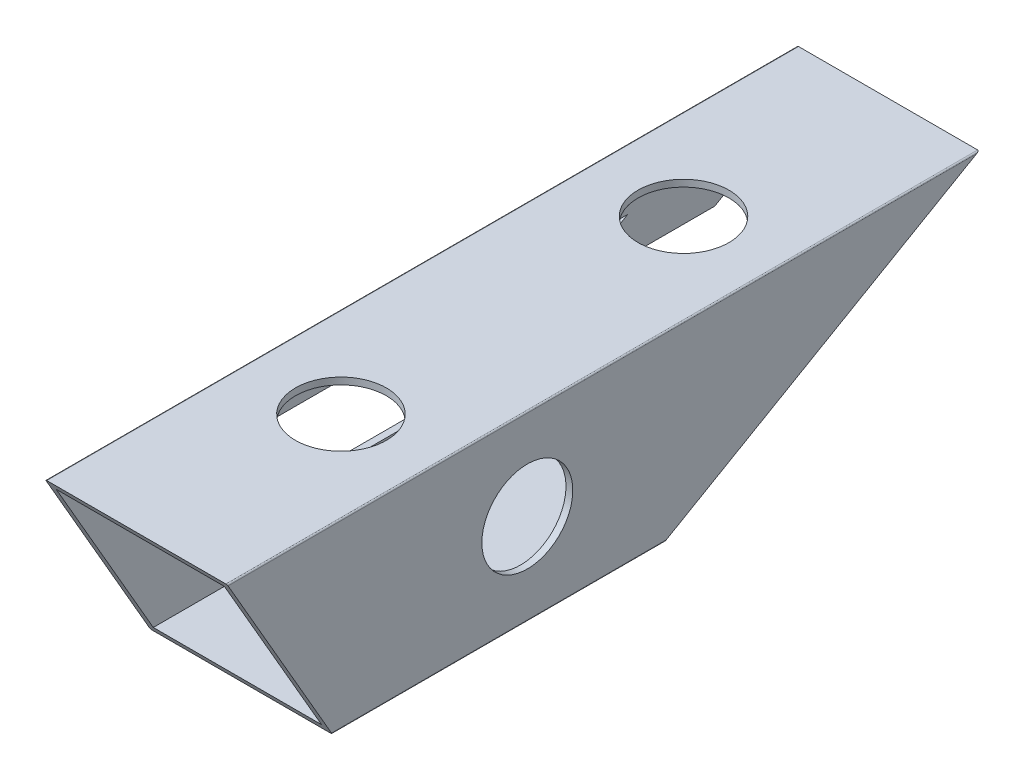
SolidWorks part; units mm, degrees
ref_plane "Front Plane" through (0, 0, 0) normal (0, 0, 1) x (1, 0, 0)
ref_plane "Top Plane" through (0, 0, 0) normal (0, 1, 0) x (1, 0, 0)
ref_plane "Right Plane" through (0, 0, 0) normal (1, 0, 0) x (0, 0, -1)
sketch "Sketch1" plane through (0, 0, 0) normal (0, 0, 1) x (1, 0, 0)
  line L0 (1.5, 1.5) -> (38.5, 1.5)
  line L1 (0.305, 0) -> (39.695, 0)
  line L2 (0, 0.305) -> (0, 39.695)
  line L3 (0.305, 40) -> (39.695, 40)
  line L4 (40, 0.305) -> (40, 39.695)
  line L5 (38.5, 1.5) -> (38.5, 38.5)
  line L6 (1.5, 38.5) -> (38.5, 38.5)
  line L7 (1.5, 1.5) -> (1.5, 38.5)
  arc A0 (0, 39.695) -> (0.305, 40) centre (0.305, 39.695) cw
  arc A1 (0.305, 0) -> (0, 0.305) centre (0.305, 0.305) cw
  arc A2 (39.695, 0) -> (40, 0.305) centre (39.695, 0.305) ccw
  arc A3 (39.695, 40) -> (40, 39.695) centre (39.695, 39.695) cw
  arc A4 (38.5, 1.5) -> (38.5, 1.5) centre (38.5, 1.5) ccw
  arc A5 (38.5, 38.5) -> (38.5, 38.5) centre (38.5, 38.5) cw
  arc A6 (1.5, 38.5) -> (1.5, 38.5) centre (1.5, 38.5) cw
  arc A7 (1.5, 1.5) -> (1.5, 1.5) centre (1.5, 1.5) cw
  point P9 (0, 0)
  dimension "D3" = 0.305
  dimension "D1" = 40
  dimension "D2" = 40
  dimension "D4" = 1.5
extrude "Boss-Extrude1" add sketch "Sketch1" along normal blind 165.35
sketch "Sketch2" plane through (40, 0, 0) normal (1, 0, 0) x (0, 0, -1)
  line L0 (0, 40) -> (-69.282, 0)
  line L1 (-165.35, 0) -> (0, 0) construction
  line L2 (-69.282, 0) -> (0, 0)
  line L3 (0, 0) -> (0, 40)
  line L4 (-165.35, 40) -> (-142.256, 0)
  line L5 (-142.256, 0) -> (-165.35, 0)
  line L6 (-165.35, 0) -> (-165.35, 40)
  dimension "D1" = 60
  dimension "D2" = 30
extrude "Cut-Extrude1" cut sketch "Sketch2" against normal blind 50
sketch "Sketch3" plane through (0, 0, 0) normal (-1, 0, 0) x (0, 0, 1)
  line L0 (69.282, 0) -> (52.282, 0)
  line L1 (52.282, 0) -> (52.282, 1.5)
  line L2 (52.282, 1.5) -> (66.684, 1.5)
  line L3 (0.5283, 39.695) -> (68.7537, 0.305) construction
  line L4 (66.684, 1.5) -> (69.282, 0)
  dimension "D1" = 1.5
  dimension "D2" = 17
extrude "Boss-Extrude2" add sketch "Sketch3" against normal blind 20 from offset 10 offset against normal yes
sketch "Sketch4" plane through (0, 0, 0) normal (-1, 0, 0) x (0, 0, 1)
  line L0 (2.3205, 30) -> (19.641, 20)
  line L1 (19.641, 20) -> (34.641, 20)
  line L2 (0.5283, 39.695) -> (68.7537, 0.305) construction
  line L3 (34.641, 20) -> (17.3205, 30)
  line L4 (17.3205, 30) -> (2.3205, 30)
  line L5 (165.35, 40) -> (0, 40) construction
  dimension "D1" = 10
  dimension "D2" = 10
  dimension "D3" = 15
extrude "Boss-Extrude3" add sketch "Sketch4" against normal blind 1.5
sketch "Sketch5" plane through (0, 0, 0) normal (1, 0, 0) x (0, 0, -1)
  line L0 (-38.7846, 28) -> (-66.4974, 12)
  line L5 (-66.4974, 12) -> (-131.8637, 12)
  line L6 (-131.8637, 12) -> (-141.1013, 28)
  line L7 (-141.1013, 28) -> (-38.7846, 28)
  line L9 (-0.5283, 39.695) -> (-68.7537, 0.305) construction
  line L10 (-142.4321, 0.305) -> (-165.1739, 39.695) construction
  line L12 (-165.35, 40) -> (0, 40) construction
  line L13 (-142.256, 0) -> (-69.282, 0) construction
  dimension "D1" = 9
  dimension "D2" = 15
  dimension "D3" = 12
  dimension "D4" = 12
extrude "Cut-Extrude2" cut sketch "Sketch5" along normal blind 10
sketch "Sketch6" plane through (0, 40, 0) normal (0, 1, 0) x (1, 0, 0)
  line L0 (39.695, 0) -> (0.305, 0) construction
  line L1 (39.695, -165.35) -> (0.305, -165.35) construction
  circle A0 centre (20, -120.35) radius 10
  circle A1 centre (20, -45) radius 10
  point P8 (20, 0)
  point P9 (0, 0)
  dimension "D1" = 20
  dimension "D2" = 20
  dimension "45" = 45
  dimension "D4" = 45
extrude "Cut-Extrude3" cut sketch "Sketch6" against normal blind 10
sketch "Sketch7" plane through (38.5, 0, 0) normal (-1, 0, 0) x (0, 0, 1)
  line L0 (165.35, 40) -> (0, 40) construction
  circle A0 centre (99.35, 20) radius 10
  dimension "D1" = 20
  dimension "D2" = 20
  dimension "D3" = 66
extrude "Cut-Extrude4" cut sketch "Sketch7" against normal blind 10
equation "\"D4@Sketch6\" = \"45@Sketch6\""
equation "\"D1@Sketch6\"=\"D2@Sketch6\""
